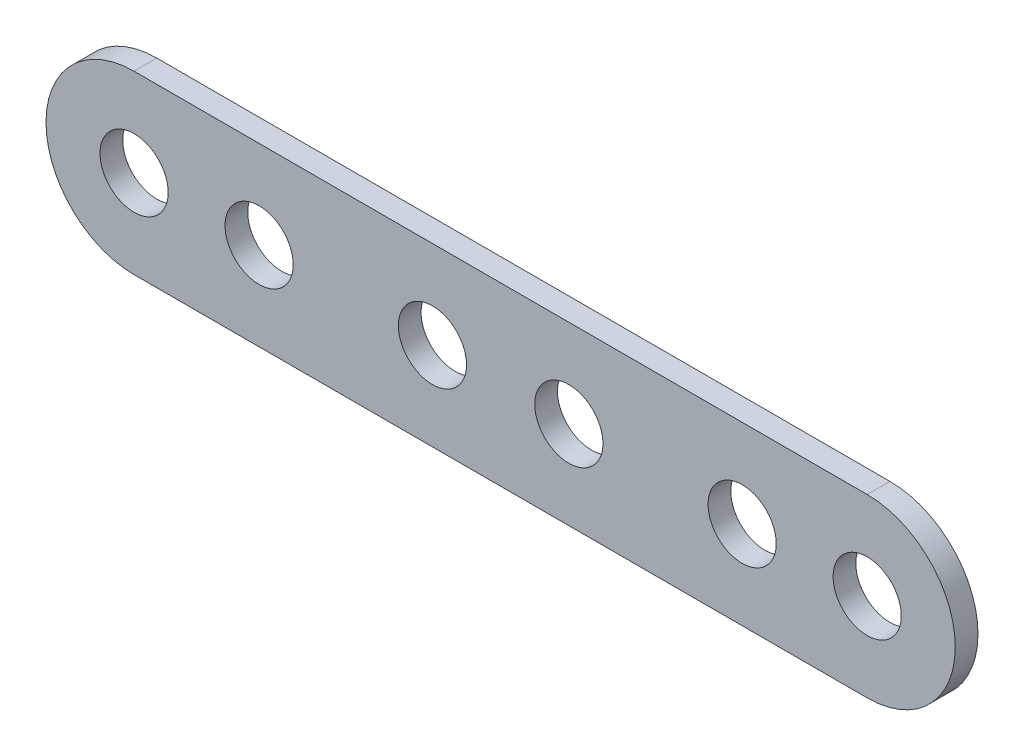
SolidWorks part; units mm, degrees
ref_plane "Спереди" through (0, 0, 0) normal (0, 0, 1) x (1, 0, 0)
ref_plane "Сверху" through (0, 0, 0) normal (0, 1, 0) x (1, 0, 0)
ref_plane "Справа" through (0, 0, 0) normal (1, 0, 0) x (0, 0, -1)
sketch "Эскиз1" plane through (0, 0, 0) normal (0, 0, 1) x (1, 0, 0)
  line L0 (32.25, 7.75) -> (-32.25, 7.75)
  line L1 (32.25, -7.75) -> (-32.25, -7.75)
  line L2 (0, 21.0997) -> (0, -20.7495) construction
  arc A0 (-32.25, 7.75) -> (-32.25, -7.75) centre (-32.25, 0) ccw
  circle A1 centre (-32.25, 0) radius 3
  circle A2 centre (-21.25, 0) radius 3
  circle A3 centre (-6, 0) radius 3
  circle A4 centre (6, 0) radius 3
  circle A5 centre (21.25, 0) radius 3
  circle A6 centre (32.25, 0) radius 3
  arc A7 (32.25, 7.75) -> (32.25, -7.75) centre (32.25, 0) cw
  point P0 (0, 0)
  point P2 (0, 7.75)
  point P21 (0, -7.75)
extrude "Бобышка-Вытянуть1" add sketch "Эскиз1" along normal blind 2
